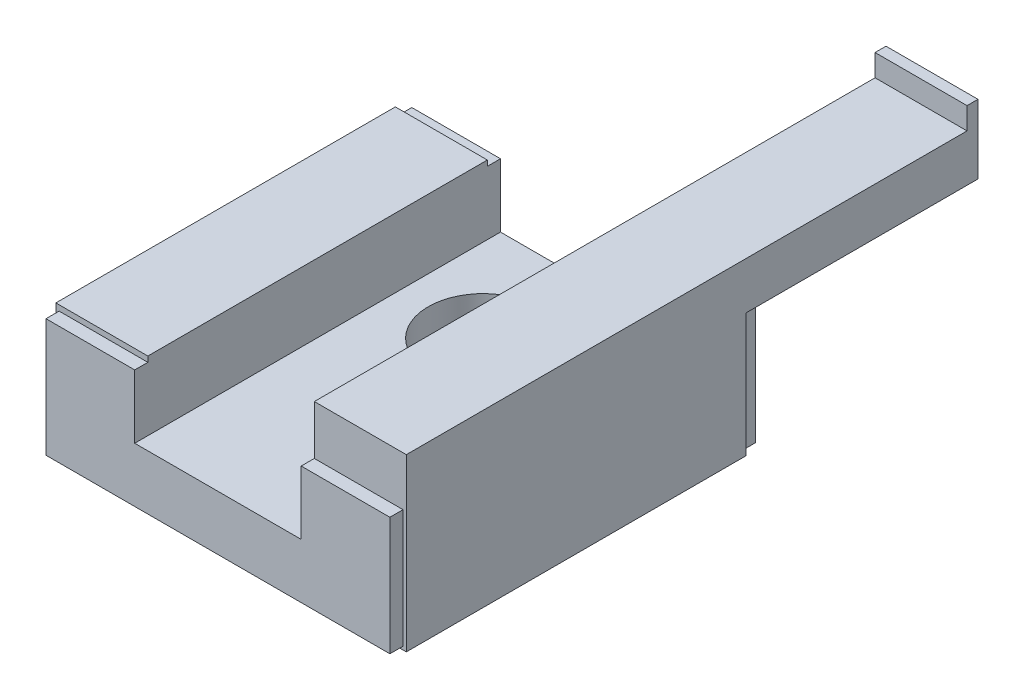
SolidWorks part; units mm, degrees
ref_plane "前视基准面" through (0, 0, 0) normal (0, 0, 1) x (1, 0, 0)
ref_plane "上视基准面" through (0, 0, 0) normal (0, 1, 0) x (1, 0, 0)
ref_plane "右视基准面" through (0, 0, 0) normal (1, 0, 0) x (0, 0, -1)
ref_plane "基准面4" through (0, 0, 0) normal (0, 0, 1) x (1, 0, 0)
sketch "草图1" plane through (0, 0, 0) normal (0, 0, 1) x (1, 0, 0)
  line L0 (-16, 0) -> (-8, 0)
  line L1 (-8, 0) -> (-7.7, 0.3)
  line L2 (-7.7, 0.3) -> (7.7, 0.3)
  line L3 (7.7, 0.3) -> (8, 0)
  line L4 (8, 0) -> (16, 0)
  line L5 (16, 0) -> (16, 15.6)
  line L6 (16, 15.6) -> (7.6, 15.6)
  line L7 (7.6, 15.6) -> (7.6, 5.3)
  line L8 (7.6, 5.3) -> (-7.6, 5.3)
  line L9 (-7.6, 5.3) -> (-7.6, 11.6)
  line L10 (-7.6, 11.6) -> (-16, 11.6)
  line L11 (-16, 11.6) -> (-16, 0)
extrude "凸台-拉伸1" add sketch "草图1" along normal blind 33.4
ref_plane "基准面5" through (0, 0, 0) normal (0, 0, 1) x (1, 0, 0)
sketch "草图2" plane through (0, 0, 0) normal (0, 0, 1) x (1, 0, 0)
  line L0 (-16, 0) -> (16, 0)
  line L1 (16, 0) -> (16, 15.6)
  line L2 (16, 15.6) -> (7.6, 15.6)
  line L3 (7.6, 15.6) -> (7.6, 11.6)
  line L4 (7.6, 11.6) -> (15.7, 11.6)
  line L5 (15.7, 11.6) -> (15.7, 0.3)
  line L6 (15.7, 0.3) -> (-15.7, 0.3)
  line L7 (-15.7, 0.3) -> (-15.7, 11.1)
  line L8 (-15.7, 11.1) -> (-7.6, 11.1)
  line L9 (-7.6, 11.1) -> (-7.6, 11.6)
  line L10 (-7.6, 11.6) -> (-16, 11.6)
  line L11 (-16, 11.6) -> (-16, 0)
extrude "切除-拉伸1" cut sketch "草图2" along normal blind 1.2
ref_plane "基准面6" through (0, 0, 33.4) normal (0, 0, 1) x (1, 0, 0)
sketch "草图3" plane through (0, 0, 33.4) normal (0, 0, 1) x (1, 0, 0)
  line L0 (-16, 0) -> (16, 0)
  line L1 (16, 0) -> (16, 15.6)
  line L2 (16, 15.6) -> (7.6, 15.6)
  line L3 (7.6, 15.6) -> (7.6, 11.1)
  line L4 (7.6, 11.1) -> (15.7, 11.1)
  line L5 (15.7, 11.1) -> (15.7, 0.3)
  line L6 (15.7, 0.3) -> (-15.7, 0.3)
  line L7 (-15.7, 0.3) -> (-15.7, 11.1)
  line L8 (-15.7, 11.1) -> (-7.6, 11.1)
  line L9 (-7.6, 11.1) -> (-7.6, 11.6)
  line L10 (-7.6, 11.6) -> (-16, 11.6)
  line L11 (-16, 11.6) -> (-16, 0)
extrude "切除-拉伸2" cut sketch "草图3" against normal blind 1.2
ref_plane "基准面7" through (0, 0, 1.2) normal (0, 0, 1) x (1, 0, 0)
sketch "草图4" plane through (0, 0, 1.2) normal (0, 0, 1) x (1, 0, 0)
  line L0 (7.6, 11.3) -> (16, 11.3)
  line L1 (16, 11.3) -> (16, 15.6)
  line L2 (16, 15.6) -> (7.6, 15.6)
  line L3 (7.6, 15.6) -> (7.6, 11.3)
extrude "凸台-拉伸2" add sketch "草图4" against normal blind 21.2
ref_plane "基准面8" through (0, 0, 8.7) normal (0, 0, 1) x (1, 0, 0)
sketch "草图5" plane through (0, 0, 8.7) normal (0, 0, 1) x (1, 0, 0)
  line L0 (12, 4) -> (13.621, 4)
  line L1 (13.621, 4) -> (13.621, 0.379)
  line L2 (13.621, 0.379) -> (14, 0)
  line L3 (14, 0) -> (12, 0)
  line L4 (12, 0) -> (12, 4)
  line L5 (12, 0) -> (12, 4) construction
revolve "切除-旋转1" cut sketch "草图5" angle 360 about L5
ref_plane "基准面9" through (0, 0, 8.7) normal (0, 0, 1) x (1, 0, 0)
sketch "草图6" plane through (0, 0, 8.7) normal (0, 0, 1) x (1, 0, 0)
  line L0 (-12, 4) -> (-10.379, 4)
  line L1 (-10.379, 4) -> (-10.379, 0.379)
  line L2 (-10.379, 0.379) -> (-10, 0)
  line L3 (-10, 0) -> (-12, 0)
  line L4 (-12, 0) -> (-12, 4)
  line L5 (-12, 0) -> (-12, 4) construction
revolve "切除-旋转2" cut sketch "草图6" angle 360 about L5
ref_plane "基准面10" through (0, 0, 24.7) normal (0, 0, 1) x (1, 0, 0)
sketch "草图7" plane through (0, 0, 24.7) normal (0, 0, 1) x (1, 0, 0)
  line L0 (12, 4) -> (13.621, 4)
  line L1 (13.621, 4) -> (13.621, 0.379)
  line L2 (13.621, 0.379) -> (14, 0)
  line L3 (14, 0) -> (12, 0)
  line L4 (12, 0) -> (12, 4)
  line L5 (12, 0) -> (12, 4) construction
revolve "切除-旋转3" cut sketch "草图7" angle 360 about L5
ref_plane "基准面11" through (0, 0, 24.7) normal (0, 0, 1) x (1, 0, 0)
sketch "草图8" plane through (0, 0, 24.7) normal (0, 0, 1) x (1, 0, 0)
  line L0 (-12, 4) -> (-10.379, 4)
  line L1 (-10.379, 4) -> (-10.379, 0.379)
  line L2 (-10.379, 0.379) -> (-10, 0)
  line L3 (-10, 0) -> (-12, 0)
  line L4 (-12, 0) -> (-12, 4)
  line L5 (-12, 0) -> (-12, 4) construction
revolve "切除-旋转4" cut sketch "草图8" angle 360 about L5
ref_plane "基准面12" through (0, 0.2, 0) normal (0, 1, 0) x (1, 0, 0)
sketch "草图9" plane through (0, 0.2, 0) normal (0, 1, 0) x (1, 0, 0)
  circle A0 centre (0, -24.7) radius 1.5
extrude "切除-拉伸3" cut sketch "草图9" along normal blind 3.1
ref_plane "基准面13" through (0, 0.2, 0) normal (0, 1, 0) x (1, 0, 0)
sketch "草图10" plane through (0, 0.2, 0) normal (0, 1, 0) x (1, 0, 0)
  circle A0 centre (0, -9.2) radius 5
extrude "切除-拉伸4" cut sketch "草图10" along normal blind 5.3
ref_plane "基准面14" through (0, 0, -20) normal (0, 0, 1) x (1, 0, 0)
sketch "草图11" plane through (0, 0, -20) normal (0, 0, 1) x (1, 0, 0)
  line L0 (7.6, 15.6) -> (16, 15.6)
  line L1 (16, 15.6) -> (16, 17.6)
  line L2 (16, 17.6) -> (7.6, 17.6)
  line L3 (7.6, 17.6) -> (7.6, 15.6)
extrude "凸台-拉伸3" add sketch "草图11" along normal blind 1
